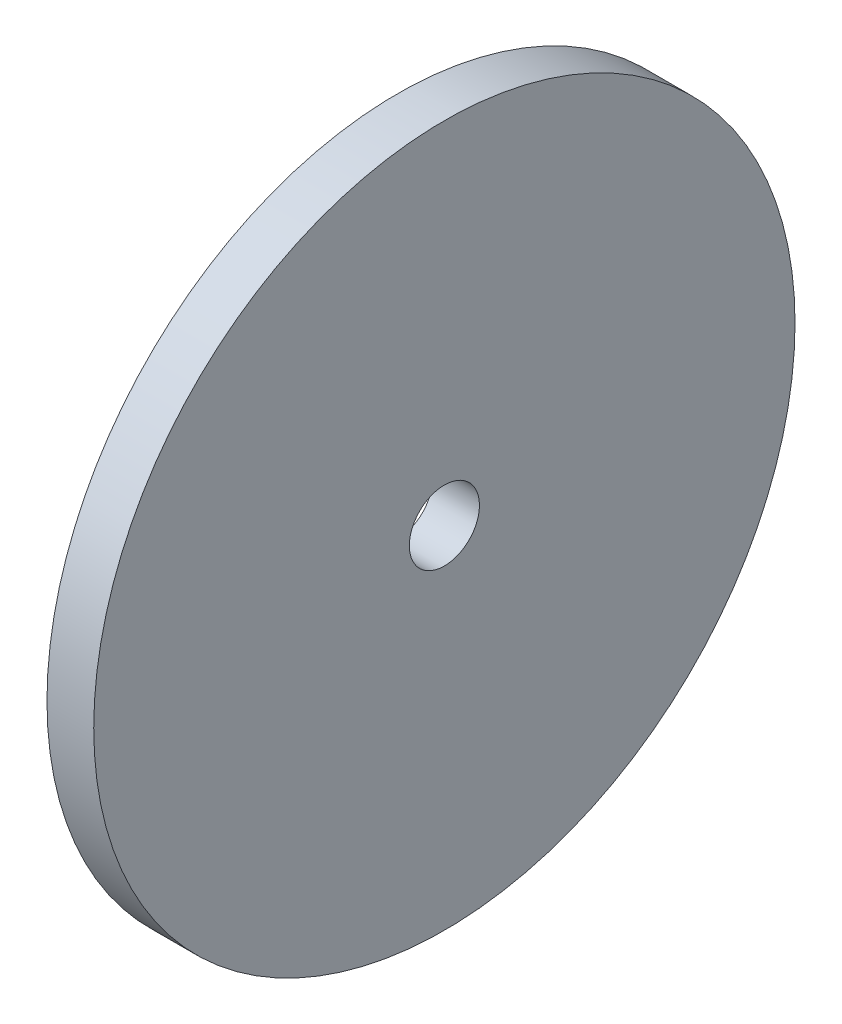
SolidWorks part; units mm, degrees
material "Pine"
ref_plane "Front Plane" through (0, 0, 0) normal (0, 0, 1) x (1, 0, 0)
ref_plane "Top Plane" through (0, 0, 0) normal (0, 1, 0) x (1, 0, 0)
ref_plane "Right Plane" through (0, 0, 0) normal (1, 0, 0) x (0, 0, -1)
sketch "Sketch1" plane through (0, 0, 0) normal (1, 0, 0) x (0, 0, -1)
  circle A0 centre (0, 0) radius 15
  dimension "D1" = 30
extrude "Boss-Extrude1" add sketch "Sketch1" along normal blind 2
sketch "Sketch2" plane through (2, 0, 0) normal (1, 0, 0) x (0, 0, -1)
  circle A1 centre (0, 0) radius 1.5
extrude "Cut-Extrude1" cut sketch "Sketch2" against normal through all
